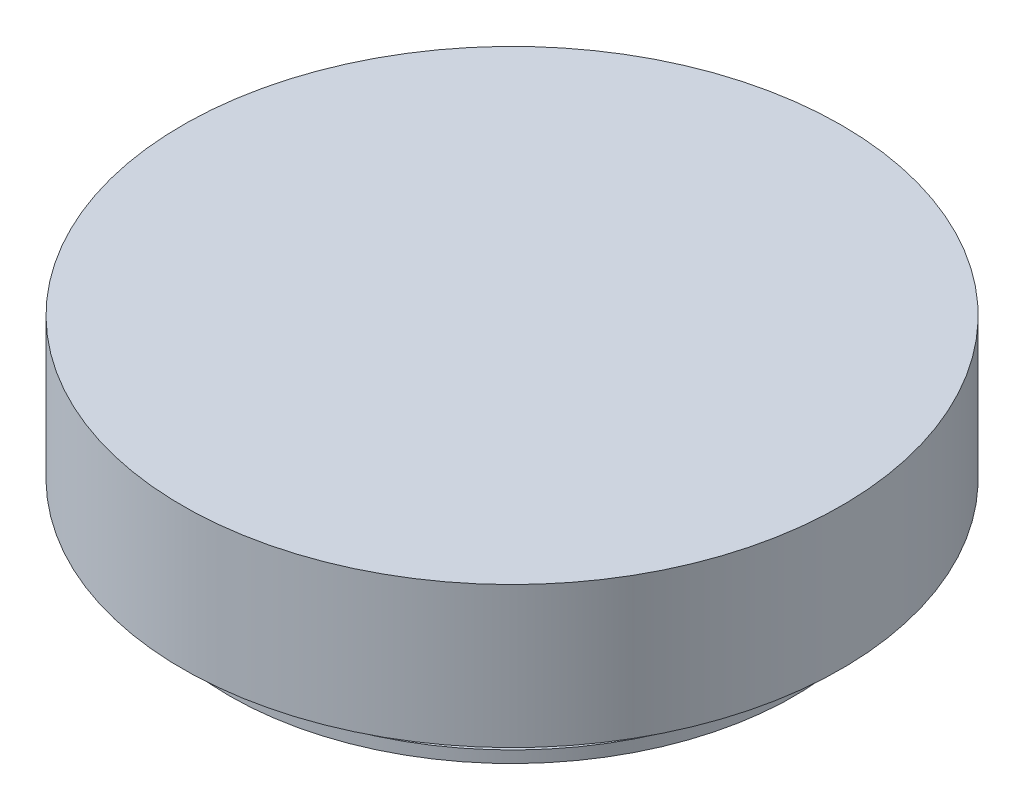
SolidWorks part; units mm, degrees
ref_plane "Front Plane" through (0, 0, 0) normal (0, 0, 1) x (1, 0, 0)
ref_plane "Top Plane" through (0, 0, 0) normal (0, 1, 0) x (1, 0, 0)
ref_plane "Right Plane" through (0, 0, 0) normal (1, 0, 0) x (0, 0, -1)
sketch "Sketch1" plane through (0, 0, 0) normal (0, 0, 1) x (1, 0, 0)
  line L0 (-38.1, 0) -> (0, 0)
  line L1 (0, 0) -> (0, 25.4)
  line L2 (0, 25.4) -> (-44.45, 25.4)
  line L3 (-44.45, 25.4) -> (-44.45, 6.35)
  line L4 (-44.45, 6.35) -> (-38.1, 6.35)
  line L5 (-38.1, 6.35) -> (-38.1, 4.3307)
  line L6 (-38.1, 4.3307) -> (-36.068, 4.3307)
  line L7 (-36.068, 4.3307) -> (-36.068, 1.5875)
  line L8 (-36.068, 1.5875) -> (-38.1, 1.5875)
  line L9 (-38.1, 1.5875) -> (-38.1, 0)
  dimension "D1" = 2.7432
  dimension "D2" = 2.032
  dimension "D3" = 6.35
  dimension "D4" = 1.5875
  dimension "D5" = 38.1
  dimension "D6" = 44.45
  dimension "D7" = 25.4
revolve "Revolve1" add sketch "Sketch1" angle 360 about L1
